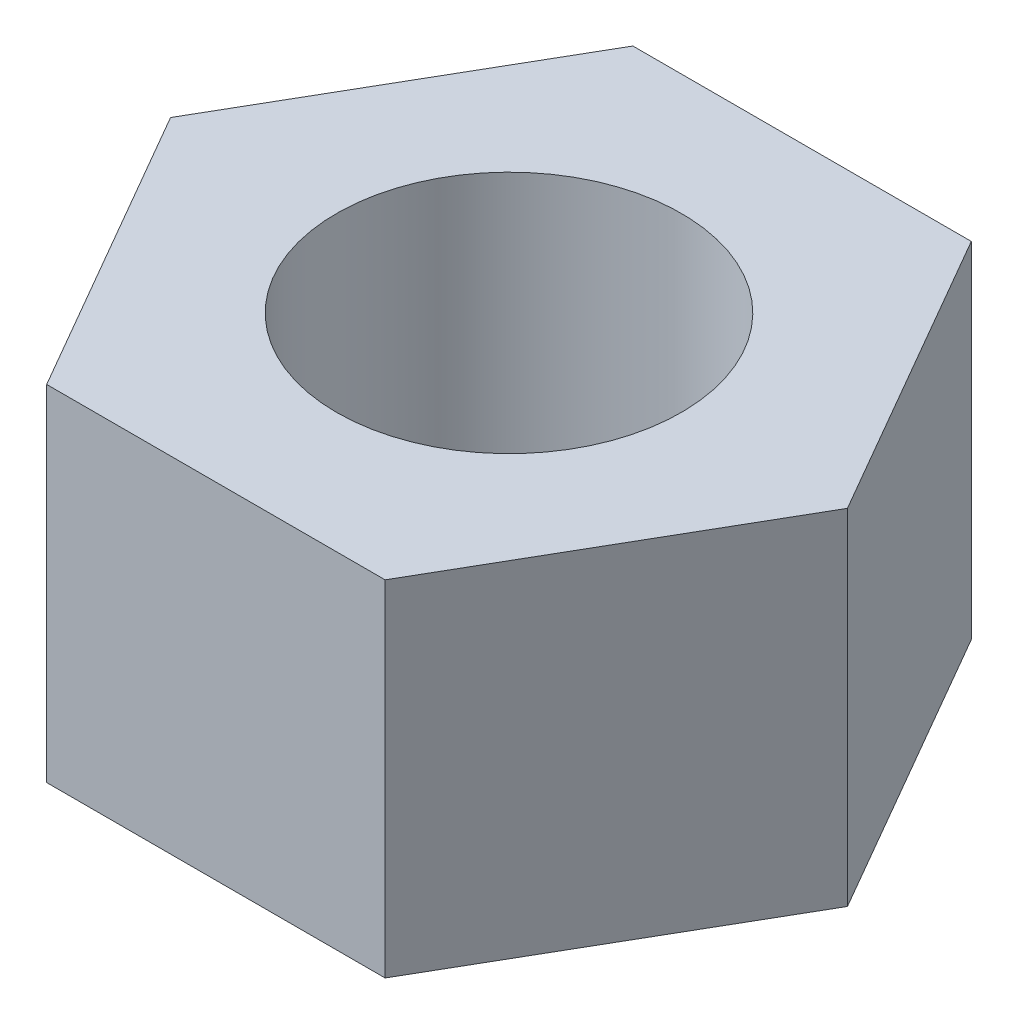
SolidWorks part; units mm, degrees
ref_plane "Front Plane" through (0, 0, 0) normal (0, 0, 1) x (1, 0, 0)
ref_plane "Top Plane" through (0, 0, 0) normal (0, 1, 0) x (1, 0, 0)
ref_plane "Right Plane" through (0, 0, 0) normal (1, 0, 0) x (0, 0, -1)
sketch "Sketch1" plane through (0, 0, 0) normal (0, 1, 0) x (1, 0, 0)
  line L1 (9.815, 0) -> (4.9075, 8.5)
  line L2 (4.9075, 8.5) -> (-4.9075, 8.5)
  line L3 (-4.9075, 8.5) -> (-9.815, 0)
  line L4 (-9.815, 0) -> (-4.9075, -8.5)
  line L5 (-4.9075, -8.5) -> (4.9075, -8.5)
  line L6 (4.9075, -8.5) -> (9.815, 0)
  circle A0 centre (0, 0) radius 8.5 construction
  circle A1 centre (0, 0) radius 5
  dimension "D1" = 10
  dimension "D2" = 17
extrude "Boss-Extrude1" add sketch "Sketch1" along normal mid plane 10
